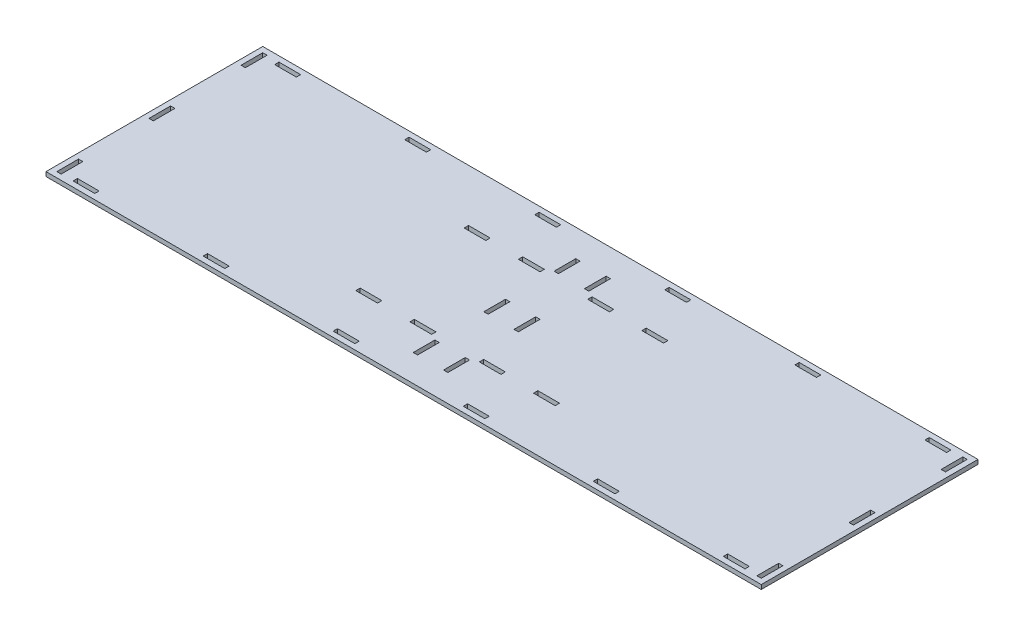
SolidWorks part; units mm, degrees
ref_plane "Front Plane" through (0, 0, 0) normal (0, 0, 1) x (1, 0, 0)
ref_plane "Top Plane" through (0, 0, 0) normal (0, 1, 0) x (1, 0, 0)
ref_plane "Right Plane" through (0, 0, 0) normal (1, 0, 0) x (0, 0, -1)
sketch "Sketch1" plane through (0, 0, 0) normal (0, 1, 0) x (1, 0, 0)
  line L0 (-12, 74.8597) -> (12, 74.8597) construction
  line L1 (0, 74.8597) -> (0, 0) construction
  line L2 (-330, -100) -> (330, -100)
  line L3 (-330, -100) -> (-330, 100)
  line L4 (-330, 100) -> (330, 100)
  line L5 (330, -100) -> (330, 100)
  line L6 (-330, -100) -> (330, 100) construction
  line L7 (-330, 100) -> (330, -100) construction
  line L8 (-92, 51.8597) -> (-72, 51.8597)
  line L9 (-92, 51.8597) -> (-92, 47.8597)
  line L10 (-92, 47.8597) -> (-72, 47.8597)
  line L11 (-72, 51.8597) -> (-72, 47.8597)
  line L12 (-42, 51.8597) -> (-22, 51.8597)
  line L13 (-42, 51.8597) -> (-42, 47.8597)
  line L14 (-42, 47.8597) -> (-22, 47.8597)
  line L15 (-22, 51.8597) -> (-22, 47.8597)
  line L16 (-92, -48.1403) -> (-72, -48.1403)
  line L17 (-92, -48.1403) -> (-92, -52.1403)
  line L18 (-92, -52.1403) -> (-72, -52.1403)
  line L19 (-72, -48.1403) -> (-72, -52.1403)
  line L20 (-42, -48.1403) -> (-22, -48.1403)
  line L21 (-42, -48.1403) -> (-42, -52.1403)
  line L22 (-42, -52.1403) -> (-22, -52.1403)
  line L23 (-22, -48.1403) -> (-22, -52.1403)
  line L24 (-16, 74.8597) -> (-12, 74.8597)
  line L25 (-16, 74.8597) -> (-16, 54.8597)
  line L26 (-16, 54.8597) -> (-12, 54.8597)
  line L27 (-12, 74.8597) -> (-12, 54.8597)
  line L28 (12, 74.8597) -> (16, 74.8597)
  line L29 (12, 74.8597) -> (12, 54.8597)
  line L30 (12, 54.8597) -> (16, 54.8597)
  line L31 (16, 74.8597) -> (16, 54.8597)
  line L32 (22, 51.8597) -> (42, 51.8597)
  line L33 (22, 51.8597) -> (22, 47.8597)
  line L34 (22, 47.8597) -> (42, 47.8597)
  line L35 (42, 51.8597) -> (42, 47.8597)
  line L36 (72, 51.8597) -> (92, 51.8597)
  line L37 (72, 51.8597) -> (72, 47.8597)
  line L38 (72, 47.8597) -> (92, 47.8597)
  line L39 (92, 51.8597) -> (92, 47.8597)
  line L40 (-16, 10) -> (-12, 10)
  line L41 (-16, 10) -> (-16, -10)
  line L42 (-16, -10) -> (-12, -10)
  line L43 (-12, 10) -> (-12, -10)
  line L44 (12, 9.8597) -> (16, 9.8597)
  line L45 (12, 9.8597) -> (12, -10.1403)
  line L46 (12, -10.1403) -> (16, -10.1403)
  line L47 (16, 9.8597) -> (16, -10.1403)
  line L48 (22, -48.1403) -> (42, -48.1403)
  line L49 (22, -48.1403) -> (22, -52.1403)
  line L50 (22, -52.1403) -> (42, -52.1403)
  line L51 (42, -48.1403) -> (42, -52.1403)
  line L52 (12, -55.1403) -> (16, -55.1403)
  line L53 (12, -55.1403) -> (12, -75.1403)
  line L54 (12, -75.1403) -> (16, -75.1403)
  line L55 (16, -55.1403) -> (16, -75.1403)
  line L56 (72, -48.1403) -> (92, -48.1403)
  line L57 (72, -48.1403) -> (72, -52.1403)
  line L58 (72, -52.1403) -> (92, -52.1403)
  line L59 (92, -48.1403) -> (92, -52.1403)
  line L60 (-325, -95) -> (-325, -75)
  line L61 (-325, -95) -> (325, -95) construction
  line L62 (-325, -95) -> (-325, 95) construction
  line L63 (-325, 95) -> (325, 95) construction
  line L64 (325, -95) -> (325, 95) construction
  line L65 (-325, -95) -> (325, 95) construction
  line L66 (-325, 95) -> (325, -95) construction
  line L67 (-325, -95) -> (-321, -95)
  line L68 (-325, 95) -> (-321, 95)
  line L69 (-325, -75) -> (-321, -75)
  line L70 (325, -75) -> (321, -75)
  line L71 (-421.8057, 0) -> (404.5887, 0) construction
  line L72 (-325, 75) -> (-325, 95)
  line L73 (-325, -10) -> (-321, -10)
  line L74 (325, -95) -> (325, -75)
  line L75 (-321, -75) -> (-321, -95)
  line L76 (-325, -10) -> (-325, 10)
  line L77 (-325, 10) -> (-321, 10)
  line L78 (-321, 10) -> (-321, -10)
  line L79 (-325, 75) -> (-321, 75)
  line L80 (-321, 95) -> (-321, 75)
  line L81 (325, -95) -> (321, -95)
  line L82 (321, -75) -> (321, -95)
  line L83 (325, -10) -> (325, 10)
  line L84 (325, 10) -> (321, 10)
  line L85 (321, 10) -> (321, -10)
  line L86 (325, -10) -> (321, -10)
  line L87 (325, 75) -> (321, 75)
  line L88 (325, 95) -> (321, 95)
  line L89 (325, 75) -> (325, 95)
  line L90 (321, 95) -> (321, 75)
  line L91 (-310, 95) -> (-290, 95)
  line L92 (-290, 95) -> (-290, 91)
  line L93 (-310, 95) -> (-310, 91)
  line L94 (-190, 95) -> (-170, 95)
  line L95 (-190, 95) -> (-190, 91)
  line L96 (-170, 95) -> (-170, 91)
  line L97 (-70, 95) -> (-70, 91)
  line L98 (-50, 95) -> (-50, 91)
  line L99 (-310, 91) -> (-290, 91)
  line L100 (-190, 91) -> (-170, 91)
  line L101 (-70, 91) -> (-50, 91)
  line L102 (310, 95) -> (310, 91)
  line L103 (-12, -55.1403) -> (-12, -75.1403)
  line L104 (-70, 95) -> (-50, 95)
  line L105 (310, 91) -> (290, 91)
  line L106 (290, 95) -> (290, 91)
  line L107 (310, 95) -> (290, 95)
  line L108 (190, 95) -> (190, 91)
  line L109 (190, 91) -> (170, 91)
  line L110 (170, 95) -> (170, 91)
  line L111 (190, 95) -> (170, 95)
  line L112 (70, 95) -> (50, 95)
  line L113 (70, 95) -> (70, 91)
  line L114 (70, 91) -> (50, 91)
  line L115 (50, 95) -> (50, 91)
  line L116 (310, -95) -> (290, -95)
  line L117 (290, -95) -> (290, -91)
  line L118 (310, -91) -> (290, -91)
  line L119 (310, -95) -> (310, -91)
  line L120 (190, -95) -> (170, -95)
  line L121 (170, -95) -> (170, -91)
  line L122 (190, -91) -> (170, -91)
  line L123 (190, -95) -> (190, -91)
  line L124 (70, -95) -> (70, -91)
  line L125 (70, -91) -> (50, -91)
  line L126 (50, -95) -> (50, -91)
  line L127 (70, -95) -> (50, -95)
  line L128 (-70, -95) -> (-50, -95)
  line L129 (-70, -95) -> (-70, -91)
  line L130 (-70, -91) -> (-50, -91)
  line L131 (-50, -95) -> (-50, -91)
  line L132 (-190, -95) -> (-190, -91)
  line L133 (-190, -91) -> (-170, -91)
  line L134 (-170, -95) -> (-170, -91)
  line L135 (-190, -95) -> (-170, -95)
  line L136 (-310, -95) -> (-310, -91)
  line L137 (-310, -91) -> (-290, -91)
  line L138 (-290, -95) -> (-290, -91)
  line L139 (-310, -95) -> (-290, -95)
  line L140 (-12, -75.1403) -> (-16, -75.1403)
  line L141 (-16, -55.1403) -> (-16, -75.1403)
  line L142 (-12, -55.1403) -> (-16, -55.1403)
  point P63 (-323, -95)
  dimension "D1" = 660
  dimension "D2" = 200
  dimension "D3" = 650
  dimension "D4" = 190
  dimension "D5" = 20
  dimension "D6" = 20
  dimension "D7" = 20
  dimension "D8" = 10
  dimension "D10" = 20
  dimension "D12" = 20
  dimension "D14" = 20
  dimension "D15" = 100
extrude "Boss-Extrude1" add sketch "Sketch1" along normal blind 4
